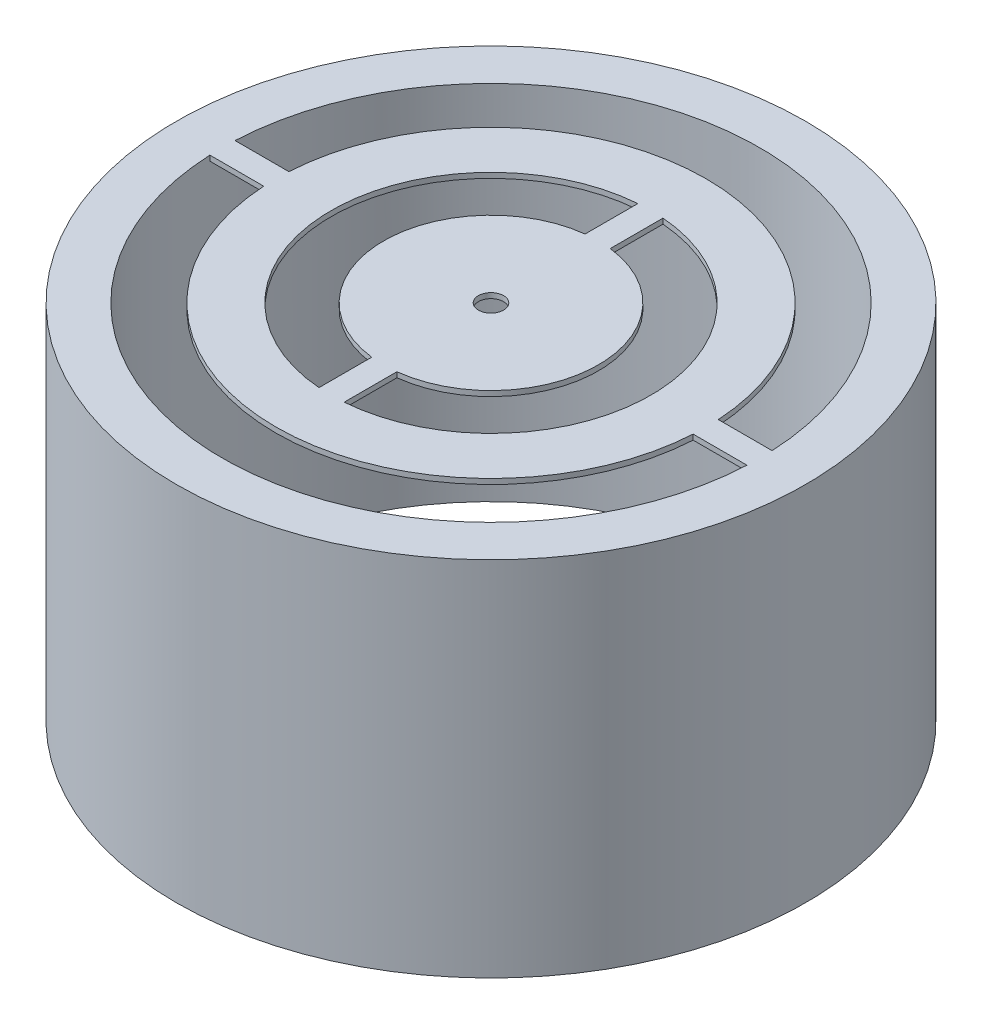
SolidWorks part; units mm, degrees
ref_plane "Front Plane" through (0, 0, 0) normal (0, 0, 1) x (1, 0, 0)
ref_plane "Top Plane" through (0, 0, 0) normal (0, 1, 0) x (1, 0, 0)
ref_plane "Right Plane" through (0, 0, 0) normal (1, 0, 0) x (0, 0, -1)
sketch "Sketch1" plane through (0, 0, 0) normal (0, 1, 0) x (1, 0, 0)
  line L0 (0, 0.6) -> (14.988, 0.6) construction
  line L1 (-12.8017, 0.6) -> (-10.2352, 0.6)
  line L2 (14.988, 0.6) -> (-14.988, 0.6) construction
  line L3 (10.2352, 0.6) -> (12.8017, 0.6)
  line L4 (-15, 0) -> (15, 0) construction
  line L5 (0.6, 0) -> (0.6, 14.988) construction
  line L6 (-0.6, 0) -> (-0.6, 14.988) construction
  line L7 (-0.6, 7.6002) -> (-0.6, 5.085)
  line L8 (0.6, 5.085) -> (0.6, 7.6002)
  line L9 (0.6, -5.085) -> (0.6, -7.6002)
  line L10 (-0.6, -7.6002) -> (-0.6, -5.085)
  line L11 (-12.8017, -0.6) -> (-10.2352, -0.6)
  line L12 (10.2352, -0.6) -> (12.8017, -0.6)
  circle A0 centre (0, 0) radius 15
  circle A5 centre (0, 0) radius 0.6
  arc A6 (-12.8017, 0.6) -> (12.8017, 0.6) centre (0, 0) cw
  arc A7 (-10.2352, 0.6) -> (10.2352, 0.6) centre (0, 0) cw
  arc A8 (-0.6, 7.6002) -> (-0.6, -7.6002) centre (0, 0) ccw
  arc A9 (0.6, 7.6002) -> (0.6, -7.6002) centre (0, 0) cw
  arc A10 (-0.6, 5.085) -> (-0.6, -5.085) centre (0, 0) ccw
  arc A11 (0.6, 5.085) -> (0.6, -5.085) centre (0, 0) cw
  arc A12 (-10.2352, -0.6) -> (10.2352, -0.6) centre (0, 0) ccw
  arc A13 (-12.8017, -0.6) -> (12.8017, -0.6) centre (0, 0) ccw
extrude "Boss-Extrude1" add sketch "Sketch1" along normal blind 0.25
sketch "Sketch2" plane through (0, 0.25, 0) normal (0, 1, 0) x (1, 0, 0)
  circle A0 centre (0, 0) radius 15
  circle A1 centre (0, 0) radius 12.8157
  dimension "D1" = 30
  dimension "D2" = 25.6315
extrude "Boss-Extrude2" add sketch "Sketch2" against normal blind 17.268
sketch "Sketch3" plane through (0, 0.25, 0) normal (0, 1, 0) x (1, 0, 0)
  line L0 (-0.6, 5.085) -> (-0.6, 10.2352)
  line L1 (0.6, 5.085) -> (0.6, 10.2352)
  line L2 (-0.6, -5.085) -> (-0.6, -10.2352)
  line L3 (0.6, -5.085) -> (0.6, -10.2352)
  line L4 (-12.8017, 0.6) -> (-8.872, 0.6)
  line L5 (-12.8017, -0.6) -> (-8.872, -0.6)
  line L6 (8.872, 0.6) -> (12.8017, 0.6)
  line L7 (12.8017, -0.6) -> (8.872, -0.6)
  line L8 (-1.1, 10.2352) -> (-1.1, 6.9083) construction
  line L9 (15, 0) -> (-15, 0) construction
  line L10 (0, -15) -> (0, 15) construction
  line L11 (-12.8017, 1.1) -> (-9.1075, 1.1) construction
  line L12 (-1.1, 7.5441) -> (-1.1, 10.2352)
  line L13 (-1.1, -7.5441) -> (-1.1, -10.2352)
  line L14 (-1.1, 10.2352) -> (-0.6, 10.2352)
  line L15 (-11.4807, 1.1) -> (-8.872, 1.1)
  line L16 (-8.872, 1.1) -> (-8.872, 0.6)
  line L17 (-1.1, -10.2352) -> (-0.6, -10.2352)
  line L18 (11.4807, 1.1) -> (8.872, 1.1)
  line L19 (8.872, 1.1) -> (8.872, 0.6)
  line L20 (11.4807, -1.1) -> (8.872, -1.1)
  line L21 (-11.4807, -1.1) -> (-8.872, -1.1)
  line L22 (-8.872, -1.1) -> (-8.872, -0.6)
  line L23 (-12.8017, -0.6) -> (-8.872, -0.6)
  line L24 (8.872, -0.6) -> (12.8017, -0.6)
  line L25 (8.872, -1.1) -> (8.872, -0.6)
  line L26 (1.1, -7.5441) -> (1.1, -10.2352)
  line L27 (1.1, 7.5441) -> (1.1, 10.2352)
  line L28 (1.1, 10.2352) -> (0.6, 10.2352)
  line L29 (0.6, 5.085) -> (0.6, 10.2352)
  line L30 (0.6, -5.085) -> (0.6, -10.2352)
  line L31 (1.1, -10.2352) -> (0.6, -10.2352)
  arc A1 (10.2352, 0.6) -> (-10.2352, 0.6) centre (0, 0) ccw construction
  arc A2 (-10.2352, -0.6) -> (10.2352, -0.6) centre (0, 0) ccw construction
  arc A3 (0.6, -5.085) -> (0.6, 5.085) centre (0, 0) ccw
  arc A4 (-0.6, 5.085) -> (-0.6, -5.085) centre (0, 0) ccw
  arc A5 (-0.6, 5.085) -> (-0.6, -5.085) centre (0, 0) ccw construction
  arc A6 (-12.8017, 0.6) -> (12.8017, 0.6) centre (0, 0) cw
  arc A7 (12.8017, 0.6) -> (-12.8017, 0.6) centre (0, 0) ccw construction
  circle A8 centre (0, 0) radius 15 construction
  arc A10 (-1.1, 11.4807) -> (-11.4807, 1.1) centre (0, 0) ccw
  arc A11 (-1.1, 7.5441) -> (-1.1, -7.5441) centre (0, 0) ccw
  arc A12 (-0.6, 7.6002) -> (-0.6, -7.6002) centre (0, 0) ccw construction
  arc A13 (-1.1, 11.4807) -> (11.4807, 1.1) centre (0, 0) cw
  circle A14 centre (0, 0) radius 15
  arc A15 (-1.1, -11.4807) -> (11.4807, -1.1) centre (0, 0) ccw
  arc A16 (-1.1, -11.4807) -> (-11.4807, -1.1) centre (0, 0) cw
  arc A17 (-12.8017, -0.6) -> (12.8017, -0.6) centre (0, 0) ccw
  arc A18 (1.1, 7.5441) -> (1.1, -7.5441) centre (0, 0) cw
  arc A19 (0.6, 5.085) -> (0.6, -5.085) centre (0, 0) cw
  dimension "D3" = 5.1202
  dimension "D4" = 7.6239
  dimension "D1" = 0.5
  dimension "D2" = 0.5
